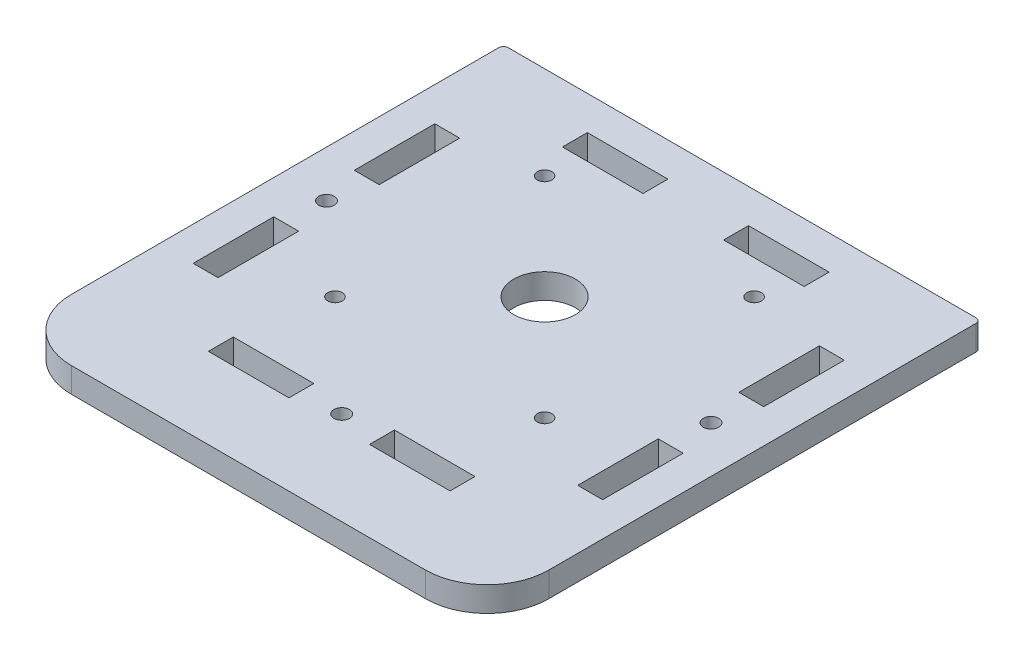
SolidWorks part; units mm, degrees
ref_plane "Front Plane" through (0, 0, 0) normal (0, 0, 1) x (1, 0, 0)
ref_plane "Top Plane" through (0, 0, 0) normal (0, 1, 0) x (1, 0, 0)
ref_plane "Right Plane" through (0, 0, 0) normal (1, 0, 0) x (0, 0, -1)
sketch "Sketch1" plane through (0, 0, 0) normal (0, 1, 0) x (1, 0, 0)
  line L1 (-81.6102, 55.1439) -> (14.7498, 55.1439)
  line L2 (-82.6102, 54.1439) -> (-82.6102, -33.8774)
  line L3 (-69.9102, -46.5774) -> (3.0498, -46.5774)
  line L4 (15.7498, 54.1439) -> (15.7498, -33.8774)
  arc A0 (15.7498, -33.8774) -> (3.0498, -46.5774) centre (3.0498, -33.8774) cw
  arc A1 (-69.9102, -46.5774) -> (-82.6102, -33.8774) centre (-69.9102, -33.8774) cw
  arc A2 (-81.6102, 55.1439) -> (-82.6102, 54.1439) centre (-81.6102, 54.1439) ccw
  arc A3 (15.7498, 54.1439) -> (14.7498, 55.1439) centre (14.7498, 54.1439) ccw
  point P8 (-82.6102, -46.5774)
  point P11 (-82.6102, 55.1439)
  point P14 (15.7498, 55.1439)
  dimension "D3" = 12.7
  dimension "D2" = 1
  dimension "D4" = 1
  dimension "D1" = 98.36
extrude "Main" add sketch "Sketch1" along normal blind 5.13
hole_wizard "Ø3.0 (3) Diameter Hole2" positions "Sketch3" profile "Sketch2" hole size "Ø3.0" standard "Ansi Metric" end condition up to next
sketch "Sketch3" plane through (0, 5.13, 0) normal (0, 1, 0) x (-1, 0, 0)
  line L0 (82.6102, -54.1439) -> (82.6102, 33.8774) construction
  line L1 (-14.7498, -55.1439) -> (81.6102, -55.1439) construction
  point P0 (55.0202, -36.0239)
  point P16 (11.8402, -36.0239)
  point P17 (55.0202, 7.1561)
  point P18 (11.8402, 7.1561)
  dimension "D3" = 27.59
  dimension "D4" = 43.18
  dimension "D5" = 19.12
  dimension "D6" = 43.18
  dimension "D1" = 2
  dimension "D2" = 2
sketch "Sketch2" plane through (-55.0202, 5.13, -36.0239) normal (1, 0, 0) x (0, 0, 1)
  line L0 (0, 0) -> (0, 5.13)
  line L1 (0, 5.13) -> (1.5, 5.13)
  line L2 (1.5, 5.13) -> (1.5, 0)
  line L5 (1.5, 0) -> (0, 0)
  line L11 (0, -6.35) -> (0, 107.95) construction
  dimension "Thru Hole Dia." = 3
  dimension "Thru Hole Depth" = 5.13
sketch "Sketch4" plane through (0, 5.13, 0) normal (0, 1, 0) x (1, 0, 0)
  line L1 (-75.6102, 34.0089) -> (-70.4802, 34.0089)
  line L2 (-75.6102, 34.0089) -> (-75.6102, 17.4089)
  line L3 (-75.6102, 17.4089) -> (-70.4802, 17.4089)
  line L4 (-70.4802, 34.0089) -> (-70.4802, 17.4089)
  line L5 (14.7498, 55.1439) -> (-81.6102, 55.1439) construction
  line L6 (3.6198, 34.0089) -> (8.7498, 34.0089)
  line L7 (3.6198, 34.0089) -> (3.6198, 17.4089)
  line L8 (3.6198, 17.4089) -> (8.7498, 17.4089)
  line L9 (8.7498, 34.0089) -> (8.7498, 17.4089)
  line L10 (-75.6102, 0.8089) -> (-70.4802, 0.8089)
  line L11 (-75.6102, 0.8089) -> (-75.6102, -15.7911)
  line L12 (-75.6102, -15.7911) -> (-70.4802, -15.7911)
  line L13 (-70.4802, 0.8089) -> (-70.4802, -15.7911)
  line L14 (3.6198, 0.8089) -> (8.7498, 0.8089)
  line L15 (3.6198, 0.8089) -> (3.6198, -15.7911)
  line L16 (-82.6102, 54.1439) -> (-82.6102, -33.8774) construction
  line L28 (3.6198, -15.7911) -> (8.7498, -15.7911)
  line L29 (8.7498, 0.8089) -> (8.7498, -15.7911)
  dimension "D1" = 16.6
  dimension "D2" = 5.13
  dimension "D5" = 7
  dimension "D6" = 21.135
  dimension "D3" = 2
  dimension "D4" = 2
extrude "Teeth holes" cut sketch "Sketch4" against normal blind 5.13
sketch "Sketch5" plane through (0, 5.13, 0) normal (0, 1, 0) x (1, 0, 0)
  line L5 (-82.6102, 54.1439) -> (-82.6102, -33.8774) construction
  line L9 (-58.3302, 48.1439) -> (-41.7302, 48.1439)
  line L10 (-58.3302, 48.1439) -> (-58.3302, 43.0139)
  line L11 (-58.3302, 43.0139) -> (-41.7302, 43.0139)
  line L12 (-41.7302, 48.1439) -> (-41.7302, 43.0139)
  line L17 (-25.1302, 48.1439) -> (-8.5302, 48.1439)
  line L18 (-25.1302, 48.1439) -> (-25.1302, 43.0139)
  line L19 (-25.1302, 43.0139) -> (-8.5302, 43.0139)
  line L20 (-8.5302, 48.1439) -> (-8.5302, 43.0139)
  line L21 (-58.3302, -24.7961) -> (-41.7302, -24.7961)
  line L22 (-58.3302, -24.7961) -> (-58.3302, -29.9261)
  line L23 (-58.3302, -29.9261) -> (-41.7302, -29.9261)
  line L24 (-41.7302, -24.7961) -> (-41.7302, -29.9261)
  line L25 (-25.1302, -24.7961) -> (-8.5302, -24.7961)
  line L26 (-25.1302, -24.7961) -> (-25.1302, -29.9261)
  line L27 (-25.1302, -29.9261) -> (-8.5302, -29.9261)
  line L28 (-8.5302, -24.7961) -> (-8.5302, -29.9261)
  dimension "D1" = 2
  dimension "D2" = 2
  dimension "D3" = 24.28
  dimension "D4" = 2
extrude "Teeth holes 2" cut sketch "Sketch5" against normal up to next
hole_wizard "1/2 (0.5) Diameter Hole1" positions "Sketch7" profile "Sketch6" hole size "1/2" standard "Ansi Inch" end condition up to next
sketch "Sketch7" plane through (0, 5.13, 0) normal (0, 1, 0) x (-1, 0, 0)
  line L0 (82.6102, -54.1439) -> (82.6102, 33.8774) construction
  line L1 (-14.7498, -55.1439) -> (81.6102, -55.1439) construction
  point P0 (33.4302, -14.4339)
  dimension "D1" = 49.18
  dimension "D2" = 40.71
sketch "Sketch6" plane through (-33.4302, 5.13, -14.4339) normal (1, 0, 0) x (0, 0, 1)
  line L0 (0, 0) -> (0, 5.13)
  line L1 (0, 5.13) -> (6.35, 5.13)
  line L2 (6.35, 5.13) -> (6.35, 0)
  line L5 (6.35, 0) -> (0, 0)
  line L11 (0, -6.35) -> (0, 107.95) construction
  dimension "Thru Hole Dia." = 12.7
  dimension "Thru Hole Depth" = 5.13
hole_wizard "M3 Clearance Hole2" positions "Sketch11" profile "Sketch10" hole size "M3" standard "Ansi Metric"
sketch "Sketch11" plane through (0, 5.13, 0) normal (0, 1, 0) x (-1, 0, 0)
  line L0 (82.6102, -54.1439) -> (82.6102, 33.8774) construction
  line L1 (-15.7498, 33.8774) -> (-15.7498, -54.1439) construction
  line L2 (75.6102, -17.4089) -> (70.4802, -17.4089) construction
  line L3 (-3.6198, -17.4089) -> (-8.7498, -17.4089) construction
  line L7 (41.7302, 24.7961) -> (58.3302, 24.7961) construction
  line L8 (41.7302, 29.9261) -> (41.7302, 24.7961) construction
  point P0 (73.0452, -9.1089)
  point P1 (-6.1848, -9.1089)
  point P7 (73.0452, -17.4089)
  point P25 (33.4302, 27.3611)
  dimension "D1" = 9.565
  dimension "D2" = 9.565
  dimension "D3" = 8.3
  dimension "D4" = 8.3
  dimension "D5" = 2.565
  dimension "D6" = 8.3
sketch "Sketch10" plane through (-73.0452, 5.13, -9.1089) normal (1, 0, 0) x (0, 0, 1)
  line L0 (0, 0) -> (0, 6.0414)
  line L1 (0, 6.0414) -> (1.6, 5.08)
  line L2 (1.6, 5.08) -> (1.6, 0)
  line L5 (1.6, 0) -> (0, 0)
  line L10 (0, 6.0414) -> (-1.6, 5.08) construction
  line L11 (0, -6.35) -> (0, 107.95) construction
  dimension "Hole Dia." = 3.2
  dimension "Hole Depth" = 5.08
  dimension "Drill Angle" = 118
hole_wizard "DELETE ME Ø3.0 (3) Diameter Hole1" [suppressed] positions "Sketch13" profile "Sketch12" hole size "Ø3.0" standard "Ansi Metric"
sketch "Sketch13" plane through (0, 5.13, 0) normal (0, 1, 0) x (-1, 0, 0)
  line L0 (58.3302, -43.0139) -> (41.7302, -43.0139) construction
  line L1 (82.6102, -54.1439) -> (82.6102, 33.8774) construction
  point P0 (52.4802, -33.4889)
  dimension "D1" = 9.525
  dimension "D2" = 30.13
sketch "Sketch12" plane through (-52.4802, 5.13, -33.4889) normal (1, 0, 0) x (0, 0, 1)
  line L0 (0, 0) -> (0, 6.0013)
  line L1 (0, 6.0013) -> (1.5, 5.1)
  line L2 (1.5, 5.1) -> (1.5, 0)
  line L5 (1.5, 0) -> (0, 0)
  line L10 (0, 6.0013) -> (-1.5, 5.1) construction
  line L11 (0, -6.35) -> (0, 107.95) construction
  dimension "Hole Dia." = 3
  dimension "Hole Depth" = 5.1
  dimension "Drill Angle" = 118
pattern_linear "LPattern1" [suppressed] count 2 spacing 38.1 count 2 spacing 38.1
equation "\"D3@Sketch3\" = (\"D1@Sketch1\"-\"D4@Sketch3\")/2"
equation "\"D1@Sketch7\" = \"D1@Sketch1\"/2"
equation "\"D2@Sketch7\" = \"D5@Sketch3\"+(0.5*\"D6@Sketch3\")"
equation "\"D3@Sketch5\" =(\"D1@Sketch1\"-\"D4@Sketch5\")/2"
equation "\"D2@Sketch13\" = (\"D1@Sketch1\"-\"RD2@Annotations\")/2"
